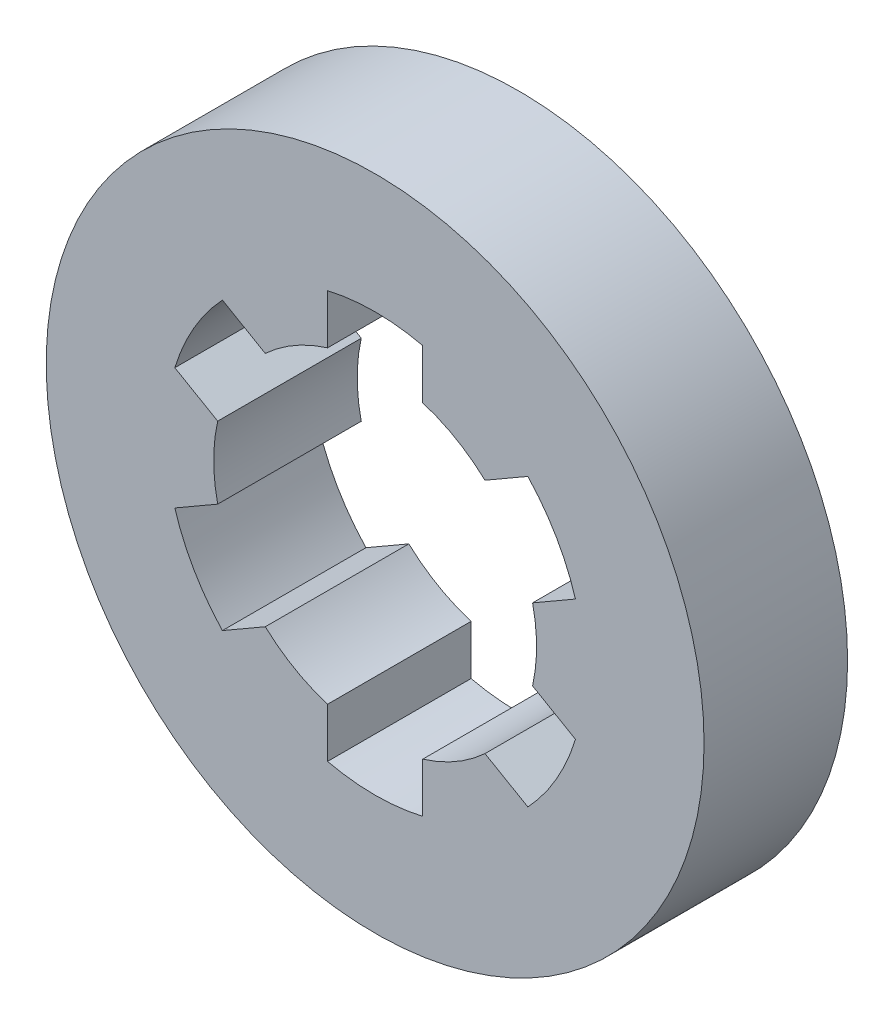
SolidWorks part; units mm, degrees
ref_plane "Front Plane" through (0, 0, 0) normal (0, 0, 1) x (1, 0, 0)
ref_plane "Top Plane" through (0, 0, 0) normal (0, 1, 0) x (1, 0, 0)
ref_plane "Right Plane" through (0, 0, 0) normal (1, 0, 0) x (0, 0, -1)
sketch "Sketch1" plane through (0, 0, 0) normal (0, 0, 1) x (1, 0, 0)
  line L1 (-3.9773, 12.9008) -> (-3.9773, 17.042)
  line L2 (3.9773, 17.042) -> (3.9773, 12.9008)
  line L3 (9.1838, 9.8948) -> (12.7702, 11.9654)
  line L4 (16.7475, 5.0766) -> (13.1611, 3.006)
  line L5 (13.1611, -3.006) -> (16.7475, -5.0766)
  line L6 (12.7702, -11.9654) -> (9.1838, -9.8948)
  line L7 (3.9773, -12.9008) -> (3.9773, -17.042)
  line L8 (-3.9773, -17.042) -> (-3.9773, -12.9008)
  line L9 (-9.1838, -9.8948) -> (-12.7702, -11.9654)
  line L10 (-16.7475, -5.0766) -> (-13.1611, -3.006)
  line L11 (-13.1611, 3.006) -> (-16.7475, 5.0766)
  line L12 (-12.7702, 11.9654) -> (-9.1838, 9.8948)
  arc A0 (-3.9773, 12.9008) -> (-9.1838, 9.8948) centre (0, 0) ccw
  circle A1 centre (0, 0) radius 27.5
  arc A2 (-16.7475, -5.0766) -> (-12.7702, -11.9654) centre (0, 0) ccw
  arc A3 (9.1838, 9.8948) -> (3.9773, 12.9008) centre (0, 0) ccw
  arc A4 (13.1611, -3.006) -> (13.1611, 3.006) centre (0, 0) ccw
  arc A5 (3.9773, -12.9008) -> (9.1838, -9.8948) centre (0, 0) ccw
  arc A6 (-9.1838, -9.8948) -> (-3.9773, -12.9008) centre (0, 0) ccw
  arc A7 (-13.1611, 3.006) -> (-13.1611, -3.006) centre (0, 0) ccw
  arc A8 (-12.7702, 11.9654) -> (-16.7475, 5.0766) centre (0, 0) ccw
  arc A9 (3.9773, 17.042) -> (-3.9773, 17.042) centre (0, 0) ccw
  arc A10 (16.7475, 5.0766) -> (12.7702, 11.9654) centre (0, 0) ccw
  arc A11 (12.7702, -11.9654) -> (16.7475, -5.0766) centre (0, 0) ccw
  arc A12 (-3.9773, -17.042) -> (3.9773, -17.042) centre (0, 0) ccw
  point P1 (0, 17.5)
  point P32 (0, 0)
  dimension "D1" = 55
  dimension "D2" = 27
  dimension "D3" = 17.5
  dimension "D6" = 6
extrude "Boss-Extrude1" add sketch "Sketch1" along normal blind 12
